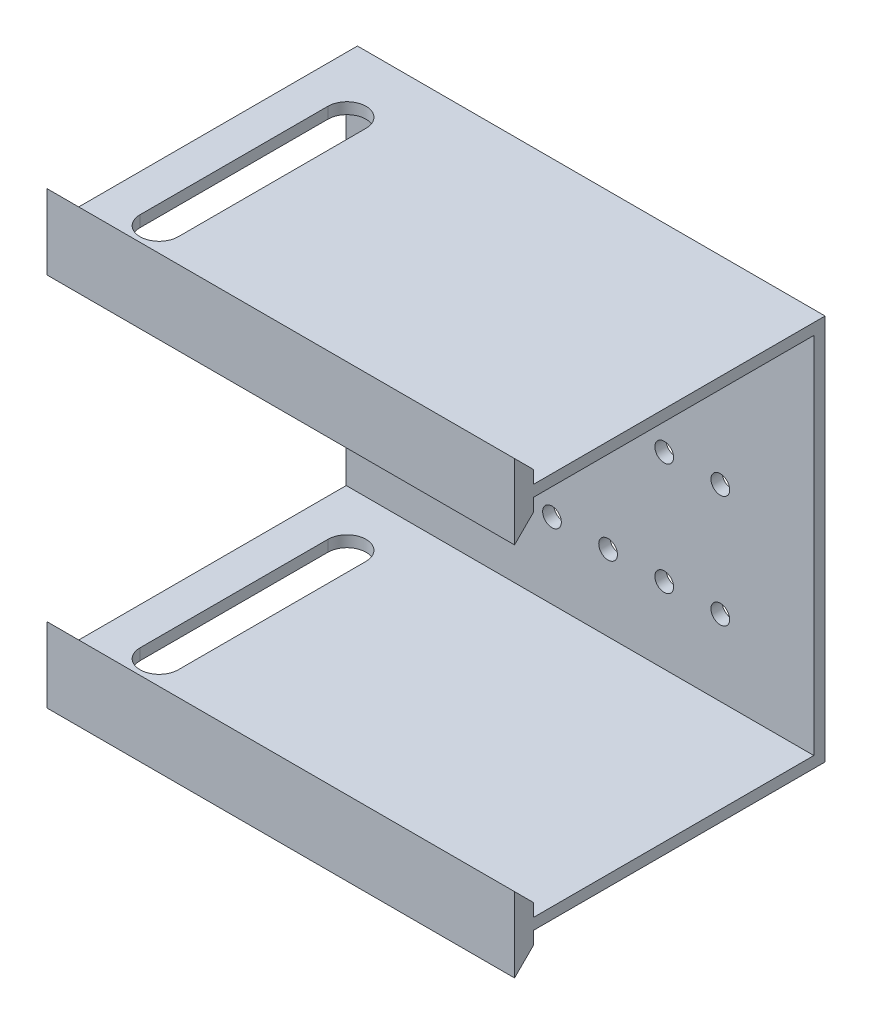
SolidWorks part; units mm, degrees
ref_plane "Plan de face" through (0, 0, 0) normal (0, 0, 1) x (1, 0, 0)
ref_plane "Plan de dessus" through (0, 0, 0) normal (0, 1, 0) x (1, 0, 0)
ref_plane "Plan de droite" through (0, 0, 0) normal (1, 0, 0) x (0, 0, -1)
sketch "Esquisse1" plane through (0, 0, 0) normal (0, 1, 0) x (1, 0, 0)
  line L0 (-10, 25.1) -> (115, 25.1) construction
  line L1 (0, 0) -> (10.2, 0)
  line L2 (0, 0) -> (0, 50.2)
  line L3 (0, 50.2) -> (10.2, 50.2)
  line L4 (10.2, 0) -> (10.2, 50.2)
  line L5 (-10, -14.9) -> (115, -14.9)
  line L6 (-10, -14.9) -> (-10, 65.1)
  line L7 (-10, 65.1) -> (115, 65.1)
  line L8 (115, -14.9) -> (115, 65.1)
  circle A0 centre (5.1, 50.2) radius 5.1
  circle A1 centre (5.1, 0) radius 5.1
  point P15 (0, 25.1)
  dimension "D1" = 50.2
  dimension "D2" = 10.2
  dimension "D3" = 10
  dimension "D4" = 80
  dimension "D5" = 125
extrude "Boss.-Extru.1" add sketch "Esquisse1" along normal blind 3 contours L6 L0 L2 A0 L4 L8 L7 | L0 L6 L5 L8 L4 A1 L2
sketch "Esquisse2" plane through (0, 0, -65.1) normal (0, 0, -1) x (-1, 0, 0)
  line L1 (10, 3) -> (-115, 3)
  line L2 (10, 3) -> (10, -100.25)
  line L3 (10, -100.25) -> (-115, -100.25)
  line L4 (-115, 3) -> (-115, -100.25)
  line L5 (-115, 3) -> (-115, 0) construction
  dimension "D1" = 103.25
extrude "Boss.-Extru.2" add sketch "Esquisse2" along normal blind 3
ref_plane "Plan2" through (0, -48.625, 0) normal (0, -1, 0) x (-1, 0, 0)
mirror "Symétrie1" about plane through (0, -48.625, 0) normal (0, -1, 0) of "Boss.-Extru.1"
sketch "Esquisse6" plane through (115, 0, 0) normal (1, 0, 0) x (0, 0, -1)
  line L0 (-9.9, 6.5) -> (-14.9, 6.5)
  line L2 (-14.9, 6.5) -> (-14.9, 11.5)
  line L4 (-14.9, 1.5) -> (68.1, 1.5) construction
  line L5 (-14.9, 3) -> (-14.9, 0) construction
  line L6 (68.1, 3) -> (68.1, -100.25) construction
  line L9 (68.1, -48.625) -> (-15, -48.625) construction
  line L18 (-14.9, 11.5) -> (-9.9, 6.5)
  line L19 (-14.9, 3) -> (-9.9, 3)
  line L20 (-14.9, 3) -> (-14.9, 6.5)
  line L21 (-14.9, 6.5) -> (-9.9, 6.5)
  line L22 (-9.9, 3) -> (-9.9, 6.5)
  line L23 (-14.9, -3.5) -> (-9.9, -3.5)
  line L24 (-9.9, 0) -> (-9.9, -3.5)
  line L25 (-14.9, 0) -> (-9.9, 0)
  line L26 (-14.9, 0) -> (-14.9, -3.5)
  line L27 (-9.9, -3.5) -> (-14.9, -3.5)
  line L28 (-14.9, -3.5) -> (-14.9, -8.5)
  line L29 (-14.9, -8.5) -> (-9.9, -3.5)
  line L30 (-14.9, -93.75) -> (-14.9, -88.75)
  line L31 (-14.9, -88.75) -> (-9.9, -93.75)
  line L32 (-9.9, -97.25) -> (-9.9, -93.75)
  line L33 (-14.9, -97.25) -> (-9.9, -97.25)
  line L34 (-14.9, -97.25) -> (-14.9, -93.75)
  line L35 (-14.9, -93.75) -> (-9.9, -93.75)
  line L36 (-14.9, -103.75) -> (-9.9, -103.75)
  line L37 (-9.9, -100.25) -> (-9.9, -103.75)
  line L38 (-14.9, -100.25) -> (-9.9, -100.25)
  line L39 (-14.9, -100.25) -> (-14.9, -103.75)
  line L40 (-9.9, -103.75) -> (-14.9, -103.75)
  line L41 (-14.9, -108.75) -> (-9.9, -103.75)
  line L42 (-14.9, -103.75) -> (-14.9, -108.75)
  line M10 (-14.9, 0) -> (65.1, 0)
  line M16 (68.1, 3) -> (-14.9, 3)
  line M24 (65.1, -97.25) -> (-14.9, -97.25)
  line M26 (-14.9, -100.25) -> (68.1, -100.25)
  dimension "D1" = 5
  dimension "D2" = 45
  dimension "D3" = 5
ref_plane "Plan1" through (0, 0, -25.1) normal (0, 0, 1) x (1, 0, 0)
extrude "Boss.-Extru.5" add sketch "Esquisse6" against normal up to surface (125 mm away) contours L35 L34 L32 M24 | L39 L36 L37 M26 | L36 L42 L41 | L30 L35 L31 | L28 L29 L23 | L26 L23 L24 M10 | L22 L0 L20 M16 | L18 L2 L0 up to face at (-10, -48.625, -25.85)
sketch "Esquisse7" plane through (0, 0, -68.1) normal (0, 0, -1) x (-1, 0, 0)
  line L0 (-115, 3) -> (-115, -100.25) construction
  line L1 (10, 3) -> (-115, 3) construction
  circle A0 centre (-90, -17) radius 2.5
  circle A1 centre (-75, -17) radius 2.5
  circle A2 centre (-60, -17) radius 2.5
  circle A3 centre (-45, -17) radius 2.5
  circle A4 centre (-30, -17) radius 2.5
  circle A5 centre (-15, -17) radius 2.5
  circle A6 centre (-75, -47) radius 2.5
  circle A7 centre (-60, -47) radius 2.5
  circle A8 centre (-45, -47) radius 2.5
  circle A9 centre (-30, -47) radius 2.5
  circle A10 centre (-15, -47) radius 2.5
  circle A11 centre (-75, -77) radius 2.5
  circle A12 centre (-60, -77) radius 2.5
  circle A13 centre (-45, -77) radius 2.5
  circle A14 centre (-30, -77) radius 2.5
  circle A15 centre (-15, -77) radius 2.5
  circle A16 centre (-90, -47) radius 2.5
  circle A17 centre (-90, -77) radius 2.5
  dimension "D1" = 5
  dimension "D2" = 25
  dimension "D3" = 20
  dimension "D4" = 6
  dimension "D5" = 3
extrude "Enlèv. mat.-Extru.2" cut sketch "Esquisse7" against normal blind 3
